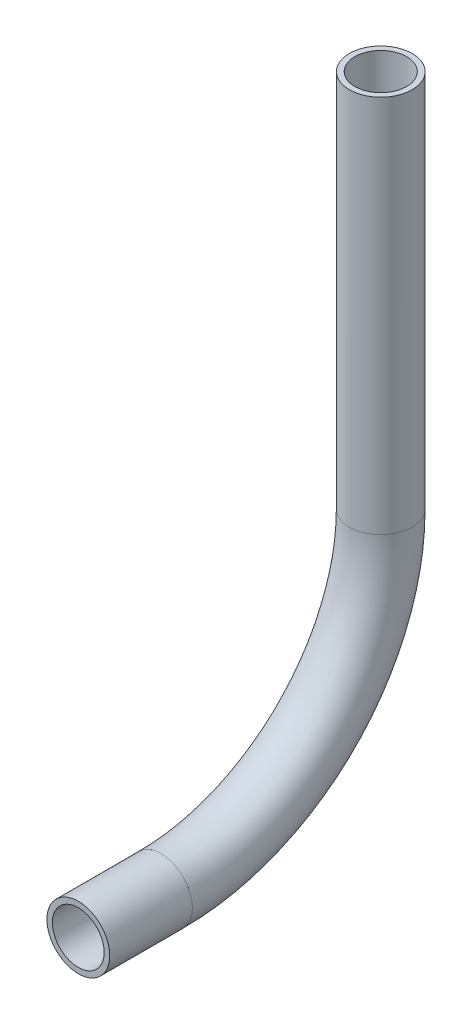
SolidWorks part; units mm, degrees
ref_plane "Front Plane" through (0, 0, 0) normal (0, 0, 1) x (1, 0, 0)
ref_plane "Top Plane" through (0, 0, 0) normal (0, 1, 0) x (1, 0, 0)
ref_plane "Right Plane" through (0, 0, 0) normal (1, 0, 0) x (0, 0, -1)
sketch "Sketch1" plane through (0, 0, 0) normal (1, 0, 0) x (0, 0, -1)
  line L0 (-303.1446, 600.0345) -> (-294.7862, 600.0345)
  line L1 (-272.5612, 622.2595) -> (-272.5612, 660.5723)
  line L2 (-303.1446, 596.8595) -> (-303.1446, 603.2095) construction
  arc A0 (-294.7862, 600.0345) -> (-272.5612, 622.2595) centre (-294.7862, 622.2595) ccw
  dimension "D1" = 22.225
other "Pipe 0.5 SCH 40(1)"
ref_plane "Plane1" through (0, 600.0345, 303.1446) normal (0, 0, -1) x (0, 1, 0)
sketch "Sketch11" plane through (0, 600.0345, 303.1446) normal (0, 0, -1) x (0, 1, 0)
  circle A0 centre (0, 0) radius 3.175
  circle A1 centre (0, 0) radius 2.6162
  point P5 (0, 0)
  dimension "In_dia" = 6.35
  dimension "Out_dia" = 5.2324
